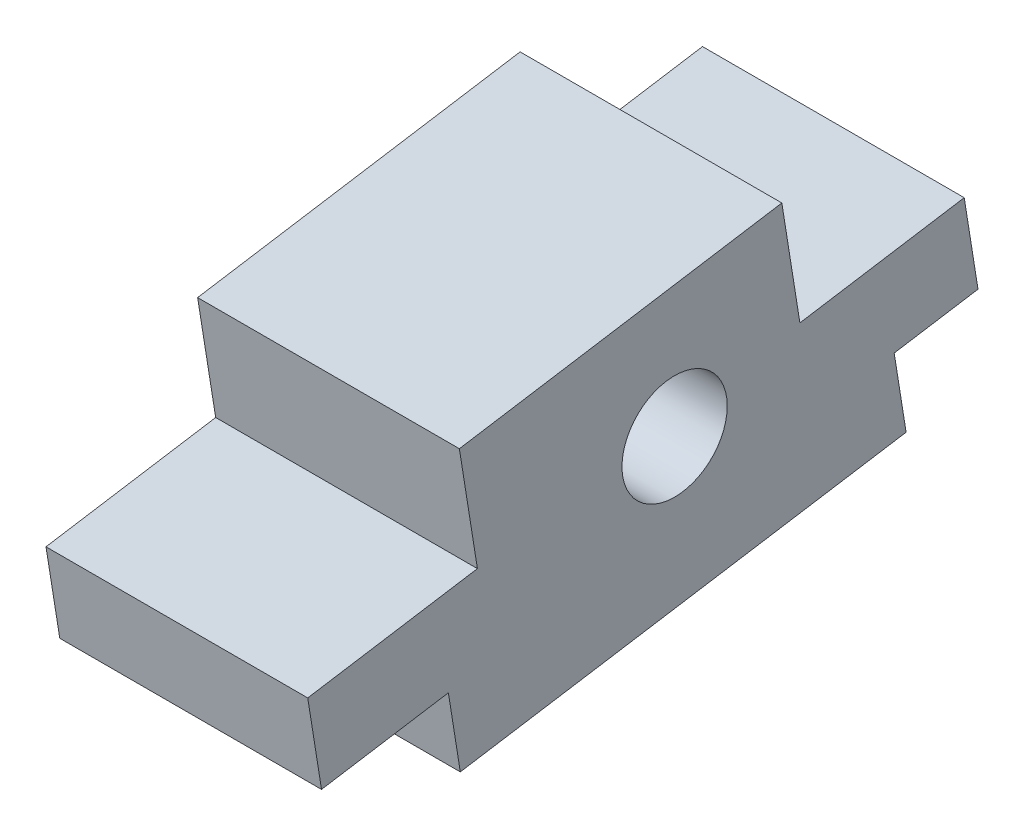
SolidWorks part; units mm, degrees
ref_plane "Front Plane" through (0, 0, 0) normal (0, 0, 1) x (1, 0, 0)
ref_plane "Top Plane" through (0, 0, 0) normal (0, 1, 0) x (1, 0, 0)
ref_plane "Right Plane" through (0, 0, 0) normal (1, 0, 0) x (0, 0, -1)
sketch "Sketch1" plane through (0, 0, 0) normal (1, 0, 0) x (0, 0, -1)
  line L0 (-40.4712, -14.8081) -> (-42.05, -4.9336)
  line L1 (-42.05, -4.9336) -> (-22.6028, -1.8242)
  line L2 (-22.6028, -1.8242) -> (-24.6714, 11.1136)
  line L3 (-24.6714, 11.1136) -> (12.2907, 17.0234)
  line L4 (12.2907, 17.0234) -> (14.3593, 4.0857)
  line L5 (14.3593, 4.0857) -> (33.1943, 7.0972)
  line L6 (33.1943, 7.0972) -> (34.7731, -2.7774)
  line L7 (34.7731, -2.7774) -> (25.1674, -4.3132)
  line L8 (25.1674, -4.3132) -> (26.5327, -12.8527)
  line L9 (26.5327, -12.8527) -> (-24.5655, -21.0228)
  line L10 (-24.5655, -21.0228) -> (-25.9308, -12.4833)
  line L11 (-25.9308, -12.4833) -> (-40.4712, -14.8081)
  line L12 (55, 0) -> (-55, 0) construction
  circle A0 centre (0, 0) radius 6.0325
  point P14 (0, 0)
  point P20 (20.2328, -4.9336)
  dimension "D13" = 12.065
  dimension "D1" = 14.8694
  dimension "D2" = 76.2
  dimension "D3" = 14.725
  dimension "D4" = 51.7472
  dimension "D5" = 19.6942
  dimension "D6" = 19.0742
  dimension "D7" = 31.75
  dimension "D8" = 8.6479
  dimension "D9" = 8.6479
  dimension "D10" = 10
  dimension "D11" = 10
  dimension "D12" = 42.3015
  dimension "D14" = 9.084
extrude "Boss-Extrude1" add sketch "Sketch1" along normal blind 30
